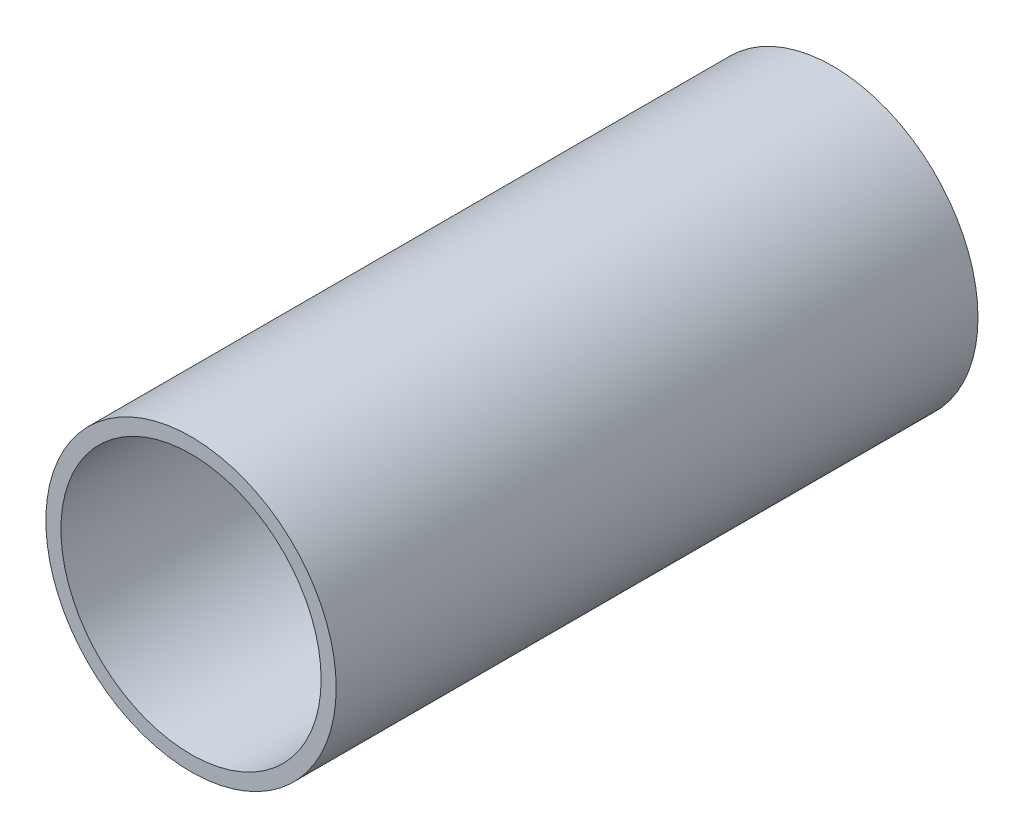
SolidWorks part; units mm, degrees
ref_plane "Front Plane" through (0, 0, 0) normal (0, 0, 1) x (1, 0, 0)
ref_plane "Top Plane" through (0, 0, 0) normal (0, 1, 0) x (1, 0, 0)
ref_plane "Right Plane" through (0, 0, 0) normal (1, 0, 0) x (0, 0, -1)
sketch "Sketch1" plane through (0, 0, 0) normal (0, 0, 1) x (1, 0, 0)
  circle A0 centre (0, 0) radius 4.826
  dimension "D1" = 9.652
extrude "Boss-Extrude1" add sketch "Sketch1" along normal blind 30.988
sketch "Sketch2" plane through (0, 0, 30.988) normal (0, 0, 1) x (1, 0, 0)
  circle A0 centre (0, 0) radius 4.325
  dimension "D1" = 8.65
extrude "Cut-Extrude1" cut sketch "Sketch2" against normal blind 37
sketch "Sketch3" plane through (0, 0, 30.988) normal (0, 0, 1) x (1, 0, 0)
  circle A0 centre (0, 0) radius 4.325 construction
  circle A1 centre (0, 0) radius 4.826 construction
  circle A2 centre (0, 0) radius 4.325
  circle A3 centre (0, 0) radius 4.826
extrude "Cut-Extrude2" cut sketch "Sketch3" against normal blind 9.652
ref_plane "Plane1" through (0, 0, 0) normal (0, 0, -1) x (-1, 0, 0)
ref_plane "Plane2" through (0, 0, 7.874) normal (0, 0, -1) x (-1, 0, 0)
sketch "Sketch5" plane through (0, 0, 7.874) normal (0, 0, -1) x (-1, 0, 0)
  circle A0 centre (0, 0) radius 4.325 construction
  circle A2 centre (0, 0) radius 4.325
  circle A4 centre (0, 0) radius 3.81
  dimension "D1" = 7.62
extrude "Boss-Extrude3" add sketch "Sketch5" against normal blind 0.635
